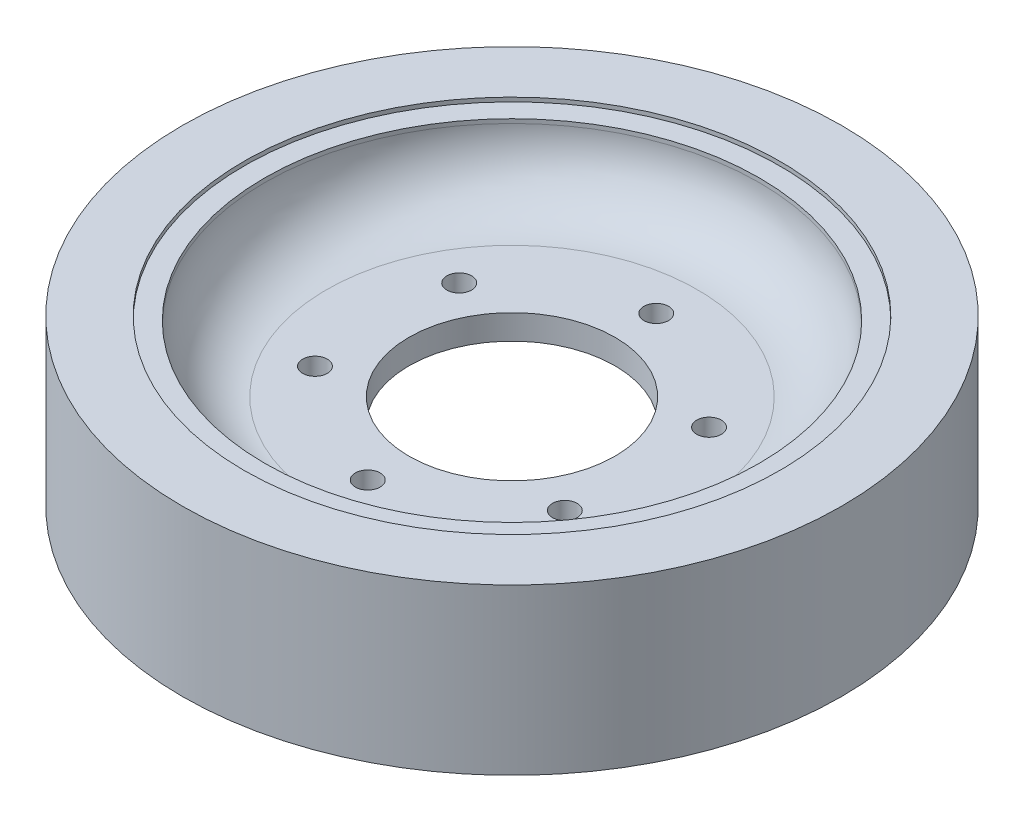
SolidWorks part; units mm, degrees
ref_plane "Front Plane" through (0, 0, 0) normal (0, 0, 1) x (1, 0, 0)
ref_plane "Top Plane" through (0, 0, 0) normal (0, 1, 0) x (1, 0, 0)
ref_plane "Right Plane" through (0, 0, 0) normal (1, 0, 0) x (0, 0, -1)
sketch "Sketch1" plane through (0, 0, 0) normal (0, 1, 0) x (1, 0, 0)
  circle A0 centre (0, 0) radius 80
  dimension "D1" = 160
extrude "Boss-Extrude1" add sketch "Sketch1" along normal blind 40
sketch "Sketch2" plane through (0, 40, 0) normal (0, 1, 0) x (1, 0, 0)
  circle A0 centre (0, 0) radius 60
  dimension "D1" = 120
extrude "Cut-Extrude1" cut sketch "Sketch2" against normal blind 17
sketch "Sketch3" plane through (0, 23, 0) normal (0, 1, 0) x (1, 0, 0)
  circle A0 centre (0, 0) radius 25
  dimension "D1" = 50
extrude "Cut-Extrude2" cut sketch "Sketch3" against normal through all
sketch "Sketch4" plane through (0, 23, 0) normal (0, 1, 0) x (1, 0, 0)
  circle A0 centre (0, 0) radius 35 construction
  circle A1 centre (0, 35) radius 3
  circle A2 centre (30.3109, 17.5) radius 3
  circle A3 centre (30.3109, -17.5) radius 3
  circle A4 centre (0, -35) radius 3
  circle A5 centre (-30.3109, -17.5) radius 3
  circle A6 centre (-30.3109, 17.5) radius 3
  point P17 (0, 0)
  dimension "D1" = 70
  dimension "D2" = 6
  dimension "D3" = 6
extrude "Cut-Extrude3" cut sketch "Sketch4" against normal through all
sketch "Sketch6" plane through (0, 0, 0) normal (0, -1, 0) x (1, 0, 0)
  circle A0 centre (0, 0) radius 60
  dimension "D1" = 120
extrude "Cut-Extrude4" cut sketch "Sketch6" against normal blind 17
sketch "Sketch7" plane through (0, 0, 0) normal (0, -1, 0) x (1, 0, 0)
  circle A0 centre (0, 0) radius 65
  dimension "D1" = 130
extrude "Cut-Extrude5" cut sketch "Sketch7" against normal blind 1
sketch "Sketch8" plane through (0, 40, 0) normal (0, 1, 0) x (1, 0, 0)
  circle A0 centre (0, 0) radius 65
  dimension "D1" = 130
extrude "Cut-Extrude6" cut sketch "Sketch8" against normal blind 1
fillet "Fillet1" radius 15 1 edges at (0, 23, 60)
fillet "Fillet2" radius 15 1 edges at (0, 17, -60)
